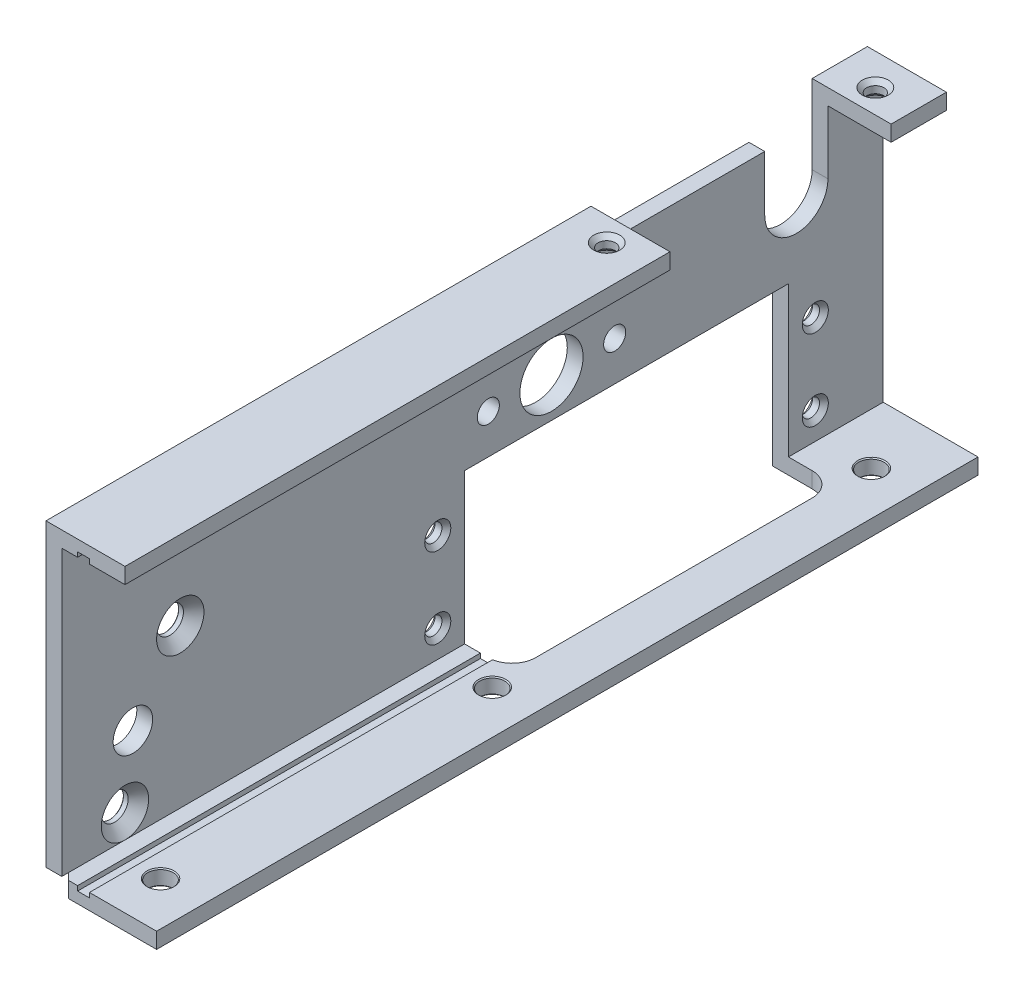
SolidWorks part; units mm, degrees
material "6063-T1"
ref_plane "Front" through (0, 0, 0) normal (0, 0, 1) x (1, 0, 0)
ref_plane "Top" through (0, 0, 0) normal (0, 1, 0) x (1, 0, 0)
ref_plane "Right" through (0, 0, 0) normal (1, 0, 0) x (0, 0, -1)
sketch "Эскиз1" plane through (0, 0, 0) normal (0, 0, 1) x (1, 0, 0)
  line L0 (0, 40) -> (0, 0)
  line L1 (0, 0) -> (20, 0)
  line L2 (2, 38) -> (2, 2)
  line L3 (2, 2) -> (20, 2)
  line L4 (2, 40) -> (2, 2) construction
  line L5 (20, 2) -> (20, 0)
  line L6 (2, 38) -> (10, 38)
  line L7 (0, 40) -> (10, 40)
  line L8 (10, 40) -> (10, 38)
  dimension "D2" = 10
  dimension "D3" = 20
  dimension "D4" = 2
  dimension "D5" = 40
  dimension "D1" = 2
extrude "Бобышка-Вытянуть1" add sketch "Эскиз1" along normal blind 104
sketch "Эскиз2" plane through (0, 0, 0) normal (0, -1, 0) x (1, 0, 0)
  line L0 (0, 53) -> (5, 53)
  line L1 (0, 104) -> (0, 0) construction
  line L2 (8, 50) -> (8, 15)
  line L3 (5, 12) -> (0, 12)
  line L4 (14, 104) -> (14, 0)
  line L5 (0, 104) -> (20, 104) construction
  line L6 (0, 0) -> (20, 0) construction
  arc A0 (8, 15) -> (5, 12) centre (5, 15) cw
  arc A1 (8, 50) -> (5, 53) centre (5, 50) ccw
  line M1 (0, 0) -> (20, 0)
  line M2 (20, 0) -> (20, 104)
  line M3 (20, 104) -> (0, 104)
  line M4 (0, 104) -> (0, 0)
  dimension "D1" = 3
  dimension "D2" = 8
  dimension "D3" = 41
  dimension "D4" = 14
  dimension "D5" = 12
extrude "Вырез-Вытянуть1" cut sketch "Эскиз2" against normal blind 21 contours L2 A1 L0 L3 A0 M4 | L4 M3 M1 M2
hole_wizard "4_отв_4-40" positions "Эскиз4" profile "Эскиз3" tap size "#4-40" standard "Ansi (в дюймах)" end condition up to next
sketch "Эскиз4" plane through (0, 0, 0) normal (-1, 0, 0) x (0, 0, 1)
  line L1 (12, 21) -> (53, 0) construction
  line L3 (12, 0) -> (53, 21) construction
  point P0 (8.6, 15.6)
  point P1 (8.6, 5.4)
  point P3 (56.4, 5.4)
  point P5 (56.4, 15.6)
  point P22 (32.5, 10.5)
  dimension "D1" = 47.8
  dimension "D2" = 10.2
  dimension "D3" = 23.9
  dimension "D4" = 5.1
sketch "Эскиз3" plane through (0, 15.6, 8.6) normal (0, 1, 0) x (0, 0, 1)
  line L0 (0, 0) -> (0, 2)
  line L1 (0, 2) -> (1.651, 2)
  line L2 (1.0922, 1.4412) -> (1.0922, 0.5588)
  line L3 (1.0922, 0.5588) -> (1.651, 0)
  line L5 (1.651, 0) -> (0, 0)
  line L6 (-1.0922, 0.5588) -> (-1.651, 0) construction
  line L7 (1.651, 2) -> (1.0922, 1.4412)
  line L8 (-1.651, 2) -> (-1.0922, 1.4412) construction
  line L11 (0, -6.35) -> (0, 107.95) construction
  dimension "Диаметр резьбы" = 2.1844
  dimension "Глубина проходного сверла" = 2
  dimension "Диаметр передней зенковки" = 3.302
  dimension "Угол передней зенковки" = 90
  dimension "Диаметр задней зенковки" = 3.302
  dimension "Угол задней зенковки" = 90
sketch "Эскиз5" plane through (2, 0, 0) normal (1, 0, 0) x (0, 0, -1)
  line L0 (-53, 21) -> (-53, 2) construction
  line L1 (-94, 4) -> (-64, 4)
  line L2 (-97, 7) -> (-97, 29)
  line L3 (-94, 32) -> (-64, 32)
  line L4 (-61, 7) -> (-61, 29)
  line L5 (-97, 4) -> (-61, 32) construction
  line L6 (-97, 32) -> (-61, 4) construction
  line L7 (-104, 0) -> (0, 0) construction
  line L8 (-12, 2) -> (-12, 21) construction
  line L9 (-50, 23) -> (-15, 23)
  line L10 (-53, 26) -> (-53, 29)
  line L11 (-50, 32) -> (-15, 32)
  line L12 (-12, 26) -> (-12, 29)
  line L13 (-53, 23) -> (-12, 32) construction
  line L14 (-53, 32) -> (-12, 23) construction
  arc A0 (-94, 4) -> (-97, 7) centre (-94, 7) cw
  arc A1 (-61, 7) -> (-64, 4) centre (-64, 7) cw
  arc A2 (-64, 32) -> (-61, 29) centre (-64, 29) cw
  arc A3 (-94, 32) -> (-97, 29) centre (-94, 29) ccw
  arc A4 (-53, 26) -> (-50, 23) centre (-50, 26) ccw
  arc A5 (-12, 26) -> (-15, 23) centre (-15, 26) cw
  arc A6 (-15, 32) -> (-12, 29) centre (-15, 29) cw
  arc A7 (-50, 32) -> (-53, 29) centre (-50, 29) ccw
  point P0 (-79, 18)
  point P21 (-32.5, 27.5)
  dimension "D3" = 3
  dimension "D6" = 3
  dimension "D1" = 36
  dimension "D2" = 28
  dimension "D4" = 8
  dimension "D5" = 4
  dimension "D7" = 9
extrude "Вырез-Вытянуть2" [suppressed] cut sketch "Эскиз5" against normal through all contours L3 A3 L2 A0 L1 A1 L4 A2
sketch "Эскиз6" plane through (0, 40, 0) normal (0, 1, 0) x (1, 0, 0)
  line L0 (10, -35) -> (-2, -35)
  line L1 (10, -104) -> (10, 0) construction
  line L2 (-5, -10) -> (-5, -32)
  line L4 (-2, -7) -> (10, -7)
  line L5 (5, -12) -> (0, -12) construction
  arc A0 (-2, -7) -> (-5, -10) centre (-2, -10) ccw
  arc A1 (-2, -35) -> (-5, -32) centre (-2, -32) cw
  dimension "D1" = 3
  dimension "D2" = 28
  dimension "D3" = 15
  dimension "D4" = 5
extrude "Вырез-Вытянуть3" cut sketch "Эскиз6" against normal blind 3
sketch "Эскиз7" plane through (2, 0, 0) normal (1, 0, 0) x (0, 0, -1)
  line L0 (-99, 25.5) -> (-99, 27.5) construction
  line L1 (-100.5, 25.5) -> (-100.5, 27.5)
  line L2 (-97.5, 25.5) -> (-97.5, 27.5)
  line L3 (0, 2) -> (0, 38) construction
  line L4 (-104, 0) -> (0, 0) construction
  arc A0 (-100.5, 25.5) -> (-97.5, 25.5) centre (-99, 25.5) ccw
  arc A1 (-97.5, 27.5) -> (-100.5, 27.5) centre (-99, 27.5) ccw
  point P2 (-99, 26.5)
  dimension "D1" = 3
  dimension "D2" = 5
  dimension "D3" = 99
  dimension "D4" = 26.5
extrude "Вырез-Вытянуть4" [suppressed] cut sketch "Эскиз7" against normal up to next
hole_wizard "Отверстие с зазором M31" positions "Эскиз9" profile "Эскиз8" hole size "M3" standard "DIN" end condition up to next
sketch "Эскиз9" plane through (0, 0, 0) normal (0, -1, 0) x (1, 0, 0)
  line L1 (0, 12) -> (0, 0) construction
  line L2 (5, 12) -> (2, 12) construction
  point P0 (8.5, 98)
  point P1 (8.5, 56)
  point P4 (8.5, 8)
  dimension "D1" = 4
  dimension "D2" = 8.5
  dimension "D3" = 48
  dimension "D4" = 42
sketch "Эскиз8" plane through (8.5, 0, 98) normal (1, 0, 0) x (0, 0, -1)
  line L0 (0, 0) -> (0, 2)
  line L1 (0, 2) -> (1.725, 2)
  line L2 (1.6, 1.875) -> (1.6, 0.125)
  line L3 (1.6, 0.125) -> (1.725, 0)
  line L5 (1.725, 0) -> (0, 0)
  line L6 (-1.6, 0.125) -> (-1.725, 0) construction
  line L7 (1.725, 2) -> (1.6, 1.875)
  line L8 (-1.725, 2) -> (-1.6, 1.875) construction
  line L11 (0, -6.35) -> (0, 107.95) construction
  dimension "Диаметр сквозного отверстия" = 3.2
  dimension "Глубина сквозного отверстия" = 2
  dimension "Диаметр передней зенковки" = 3.45
  dimension "Угол передней зенковки" = 90
  dimension "Диаметр задней зенковки" = 3.45
  dimension "Угол задней зенковки" = 90
sketch "Эскиз10" [suppressed] plane through (2, 0, 0) normal (1, 0, 0) x (0, 0, -1)
  line L0 (-58, 24) -> (-56, 24)
  line L1 (-58, 7) -> (-58, 29) construction
  line L2 (-56, 24) -> (-56, 25.6)
  line L3 (-56, 25.6) -> (-58, 25.6)
  line L4 (0, 25.6) -> (-2, 25.6)
  line L5 (0, 2) -> (0, 38) construction
  line L6 (-2, 25.6) -> (-2, 24)
  line L7 (-2, 24) -> (0, 24)
  line L8 (-104, 0) -> (0, 0) construction
  line M19 (-58, 29) -> (-58, 7)
  line M27 (0, 2) -> (0, 38)
  dimension "D1" = 1.6
  dimension "D2" = 24
  dimension "D3" = 2
extrude "Вырез-Вытянуть5" [suppressed] cut sketch "Эскиз10" against normal through all contours L2 L3 L0 M19 | L6 L7 L4 M27
hole_wizard "2_отв_4-40" positions "Эскиз12" profile "Эскиз11" tap size "#4-40" standard "Ansi (в дюймах)" end condition up to next
sketch "Эскиз12" plane through (0, 40, 0) normal (0, 1, 0) x (-1, 0, 0)
  line L0 (0, 7) -> (0, 0) construction
  line L2 (0, 7) -> (-10, 7) construction
  point P1 (-5, 38)
  point P4 (-5, 4)
  dimension "D1" = 5
  dimension "D2" = 3
  dimension "D3" = 34
sketch "Эскиз11" plane through (5, 40, 38) normal (1, 0, 0) x (0, 0, 1)
  line L0 (0, 0) -> (0, 2)
  line L1 (0, 2) -> (1.651, 2)
  line L2 (1.0922, 1.4412) -> (1.0922, 0.5588)
  line L3 (1.0922, 0.5588) -> (1.651, 0)
  line L5 (1.651, 0) -> (0, 0)
  line L6 (-1.0922, 0.5588) -> (-1.651, 0) construction
  line L7 (1.651, 2) -> (1.0922, 1.4412)
  line L8 (-1.651, 2) -> (-1.0922, 1.4412) construction
  line L11 (0, -6.35) -> (0, 107.95) construction
  dimension "Диаметр резьбы" = 2.1844
  dimension "Глубина проходного сверла" = 2
  dimension "Диаметр передней зенковки" = 3.302
  dimension "Угол передней зенковки" = 90
  dimension "Диаметр задней зенковки" = 3.302
  dimension "Угол задней зенковки" = 90
sketch "Эскиз13" plane through (0, 0, 104) normal (0, 0, 1) x (1, 0, 0)
  line L1 (4, 38.6) -> (5.5, 38.6)
  line L2 (4, 38.6) -> (4, 1.4)
  line L3 (4, 1.4) -> (5.5, 1.4)
  line L4 (5.5, 38.6) -> (5.5, 1.4)
  line L5 (2, 38) -> (10, 38) construction
  line L7 (2, 2) -> (2, 38) construction
  dimension "D1" = 37.2
  dimension "D2" = 0.6
  dimension "D3" = 1.5
  dimension "D4" = 2
extrude "Вырез-Вытянуть6" cut sketch "Эскиз13" against normal blind 54
sketch "Эскиз14" plane through (0, 0, 0) normal (-1, 0, 0) x (0, 0, 1)
  line L0 (0, 24.8) -> (5, 24.8)
  line L1 (0, 40) -> (0, 0) construction
  line L2 (5, 24.8) -> (5, 23)
  line L3 (5, 23) -> (0, 23)
  line L4 (104, 24.8) -> (99, 24.8)
  line L5 (104, 40) -> (104, 0) construction
  line L6 (99, 24.8) -> (99, 23)
  line L7 (99, 23) -> (104, 23)
  line L9 (12, 0) -> (0, 0) construction
  line M7 (0, 40) -> (0, 0)
  line M13 (104, 0) -> (104, 40)
  dimension "D1" = 1.8
  dimension "D2" = 23
  dimension "D3" = 5
extrude "Вырез-Вытянуть7" [suppressed] cut sketch "Эскиз14" against normal through all contours L3 L2 L0 M7 | L6 L7 L4 M13
hole_wizard "М3 потай" positions "Эскиз16" profile "Эскиз15" countersink size "M3" standard "Ansi (метрические)" end condition through all
sketch "Эскиз16" plane through (2, 0, 0) normal (1, 0, 0) x (0, 0, -1)
  line L0 (-104, 2) -> (-104, 38) construction
  line L1 (-104, 0) -> (0, 0) construction
  point P1 (-89, 34)
  point P4 (-89, 22)
  point P13 (-96, 35)
  point P15 (-96, 5)
  dimension "D1" = 15
  dimension "D2" = 22
  dimension "D3" = 34
  dimension "D4" = 1
  dimension "D5" = 7
  dimension "D6" = 30
sketch "Эскиз15" plane through (2, 34, 89) normal (0, 1, 0) x (0, 0, -1)
  line L0 (0, 0) -> (0, 2)
  line L1 (0, 2) -> (1.8, 2)
  line L2 (1.7, 1.9) -> (1.7, 1.3)
  line L3 (1.7, 1.3) -> (3, 0)
  line L5 (3, 0) -> (0, 0)
  line L6 (-1.7, 1.3) -> (-3, 0) construction
  line L7 (1.8, 2) -> (1.7, 1.9)
  line L8 (-1.8, 2) -> (-1.7, 1.9) construction
  line L11 (0, -6.35) -> (0, 107.95) construction
  dimension "Диаметр сквозного отверстия" = 3.4
  dimension "Глубина сквозного отверстия" = 2
  dimension "Диаметр передней зенковки" = 6
  dimension "Угол передней зенковки" = 90
  dimension "Диаметр задней зенковки" = 3.6
  dimension "Угол задней зенковки" = 90
sketch "Эскиз17" plane through (0, 0, 0) normal (0, -1, 0) x (1, 0, 0)
  line L0 (0, 104) -> (2.8284, 104)
  line L1 (0, 104) -> (14, 104) construction
  line L2 (2.8284, 104) -> (0, 101.1716)
  line L3 (0, 104) -> (0, 53) construction
  line L4 (0, 101.1716) -> (0, 104)
  dimension "D1" = 45
  dimension "D2" = 2
extrude "Вырез-Вытянуть8" cut sketch "Эскиз17" against normal blind 2
sketch "Эскиз18" plane through (2, 0, 0) normal (1, 0, 0) x (0, 0, -1)
  line L0 (-7, 37) -> (-7, 30)
  line L1 (-35, 37) -> (-7, 37) construction
  line L2 (-7, 40) -> (0, 40) construction
  line L3 (-15, 30) -> (-15, 37)
  line L6 (0, 2) -> (0, 38) construction
  line L7 (-104, 40) -> (-35, 40) construction
  circle A0 centre (-42, 26) radius 4
  circle A1 centre (-50, 26) radius 1.4
  circle A2 centre (-34, 26) radius 1.4
  arc A3 (-15, 30) -> (-7, 30) centre (-11, 30) ccw
  line M8 (-7, 37) -> (-35, 37)
  dimension "D4" = 42
  dimension "D6" = 8
  dimension "D7" = 2.8
  dimension "D8" = 16
  dimension "D9" = 8
  dimension "D1" = 8
  dimension "D2" = 7
  dimension "D3" = 10
  dimension "D5" = 14
extrude "Вырез-Вытянуть9" cut sketch "Эскиз18" against normal through all contours L3 A3 L0 M8 | A0 | A1 | A2
sketch "Эскиз19" plane through (2, 0, 0) normal (1, 0, 0) x (0, 0, -1)
  line L0 (-104, 2) -> (-104, 38) construction
  line L1 (-104, 0) -> (0, 0) construction
  circle A0 centre (-95, 13.5) radius 2.5
  dimension "D1" = 5
  dimension "D3" = 13.5
  dimension "D2" = 9
extrude "Вырез-Вытянуть10" cut sketch "Эскиз19" against normal up to next
